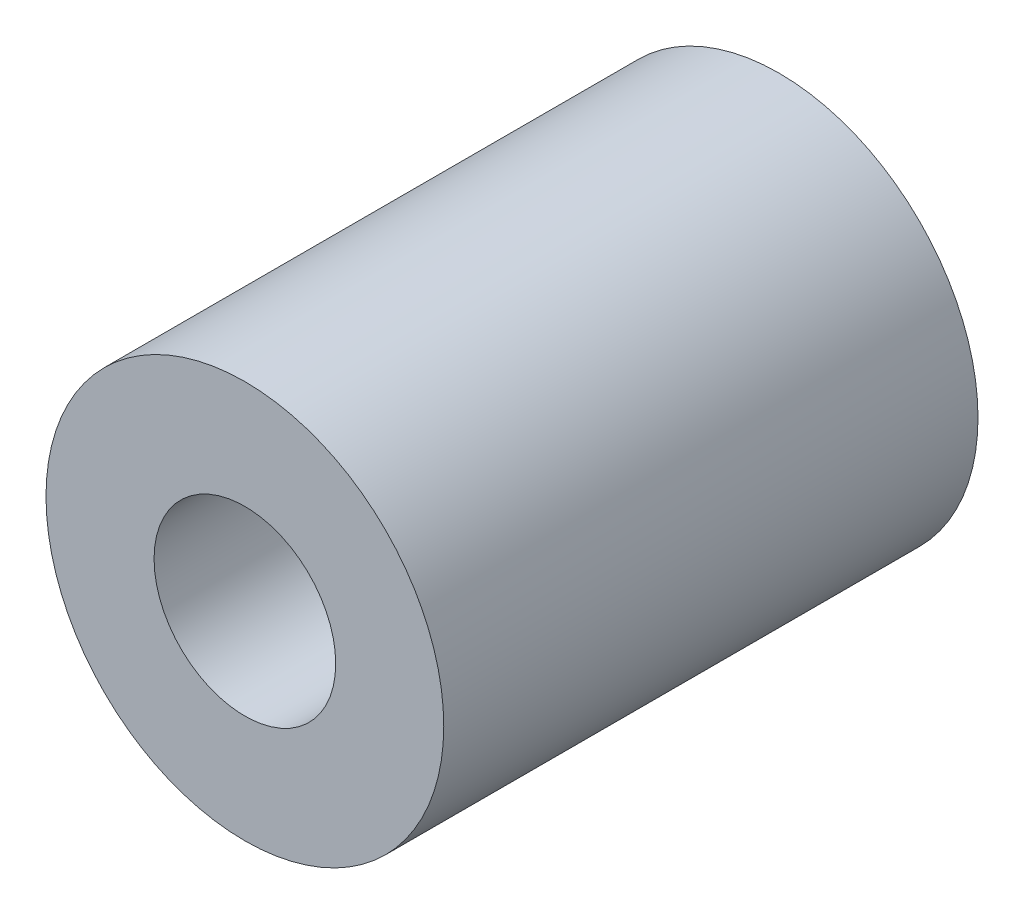
SolidWorks part; units mm, degrees
material "ABS"
ref_plane "Front Plane" through (0, 0, 0) normal (0, 0, 1) x (1, 0, 0)
ref_plane "Top Plane" through (0, 0, 0) normal (0, 1, 0) x (1, 0, 0)
ref_plane "Right Plane" through (0, 0, 0) normal (1, 0, 0) x (0, 0, -1)
sketch "Sketch1" plane through (0, 0, 0) normal (0, 0, 1) x (1, 0, 0)
  circle A0 centre (-60.5331, -24.4695) radius 5.584
extrude "Boss-Extrude1" add sketch "Sketch1" along normal blind 15
sketch "Sketch2" plane through (0, 0, 0) normal (0, 0, -1) x (-1, 0, 0)
  circle A0 centre (60.5331, -24.4695) radius 2.6
  circle A1 centre (60.5331, -24.4695) radius 5.584 construction
  dimension "D1" = 5.2
extrude "Cut-Extrude1" cut sketch "Sketch2" against normal blind 8.2
sketch "Sketch3" plane through (0, 0, 15) normal (0, 0, 1) x (1, 0, 0)
  circle A0 centre (-60.5331, -24.4695) radius 2.55
  dimension "D1" = 5.1
extrude "Cut-Extrude2" cut sketch "Sketch3" against normal blind 7
